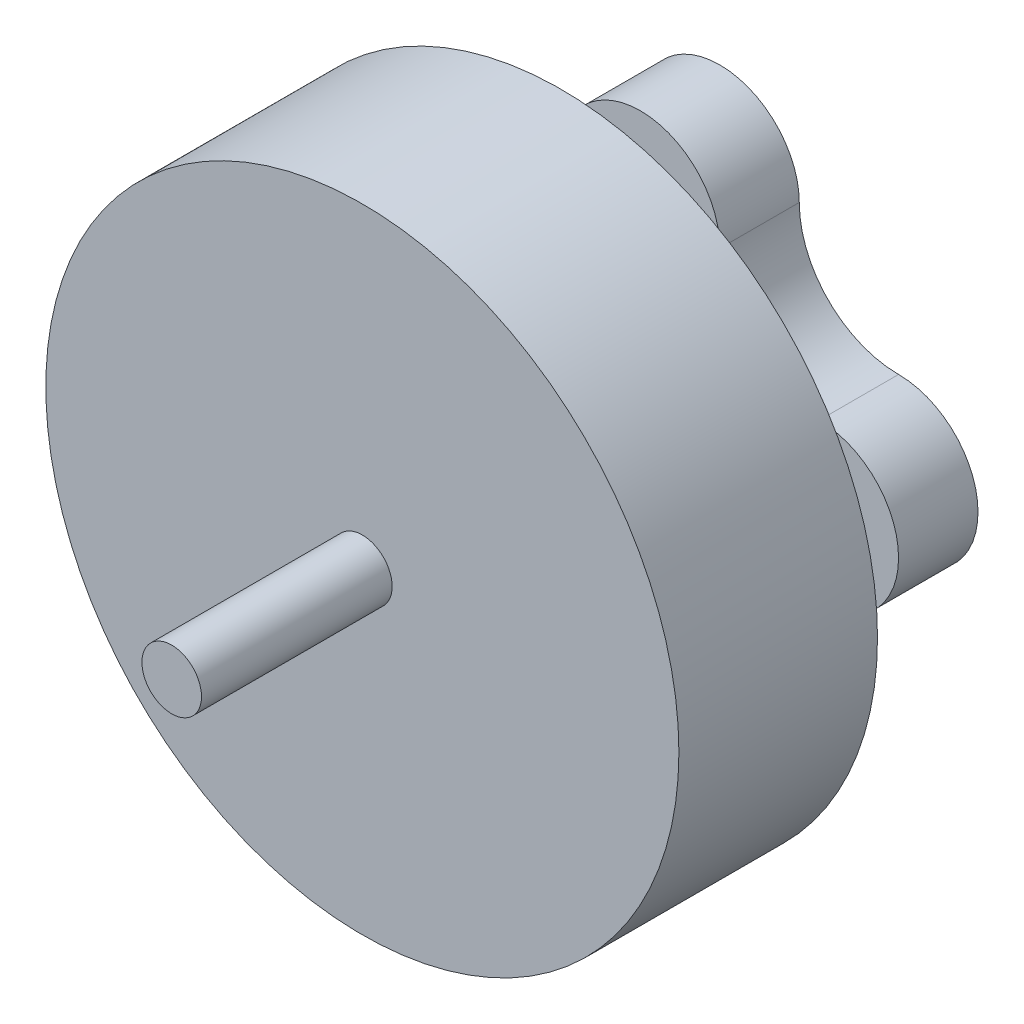
SolidWorks part; units mm, degrees
ref_plane "Front Plane" through (0, 0, 0) normal (0, 0, 1) x (1, 0, 0)
ref_plane "Top Plane" through (0, 0, 0) normal (0, 1, 0) x (1, 0, 0)
ref_plane "Right Plane" through (0, 0, 0) normal (1, 0, 0) x (0, 0, -1)
sketch "Sketch1" plane through (0, 0, 0) normal (0, 0, 1) x (1, 0, 0)
  circle A0 centre (0, 0) radius 7.97
  dimension "D1" = 15.94
extrude "motor" add sketch "Sketch1" along normal blind 5
sketch "shaft for prop" plane through (0, 0, 5) normal (0, 0, 1) x (1, 0, 0)
  circle A0 centre (0, 0) radius 0.75
  dimension "D1" = 1.5
extrude "Boss-Extrude2" add sketch "shaft for prop" along normal blind 4.8
sketch "Sketch3" plane through (0, 0, 0) normal (0, 0, -1) x (-1, 0, 0)
  circle A0 centre (0, 0) radius 2.5
  dimension "D1" = 5
extrude "Boss-Extrude3" add sketch "Sketch3" along normal blind 2
sketch "Sketch5" plane through (0, 0, -2) normal (0, 0, -1) x (-1, 0, 0)
  line L0 (-4.5, 0) -> (4.5, 0) construction
  line L1 (0, -4.5) -> (0, 4.5) construction
  circle A0 centre (4.5, 0) radius 1
  circle A1 centre (-4.5, 0) radius 1
  circle A2 centre (0, -4.5) radius 1
  circle A3 centre (0, 4.5) radius 1
  arc A4 (-4.5, 2) -> (-4.5, -2) centre (-4.5, 0) ccw
  arc A5 (4.5, 2) -> (4.5, -2) centre (4.5, 0) cw
  arc A6 (-2, -4.5) -> (2, -4.5) centre (0, -4.5) ccw
  arc A7 (-2, 4.5) -> (2, 4.5) centre (0, 4.5) cw
  arc A8 (-2, -4.5) -> (-4.5, -2) centre (-4.5, -4.5) ccw
  arc A9 (-2, 4.5) -> (-4.5, 2) centre (-4.5, 4.5) cw
  arc A10 (4.5, -2) -> (2, -4.5) centre (4.5, -4.5) ccw
  arc A11 (4.5, 2) -> (2, 4.5) centre (4.5, 4.5) cw
  point P4 (0, 0)
  point P7 (0, 0)
  dimension "D3" = 2
  dimension "D4" = 2
  dimension "D5" = 4
  dimension "D6" = 4
  dimension "D1" = 9
  dimension "D2" = 9
extrude "Boss-Extrude4" add sketch "Sketch5" along normal blind 2 contours A0 | A2 | A7 A11 A5 A10 A6 A8 A4 A9 | A1 | A3
